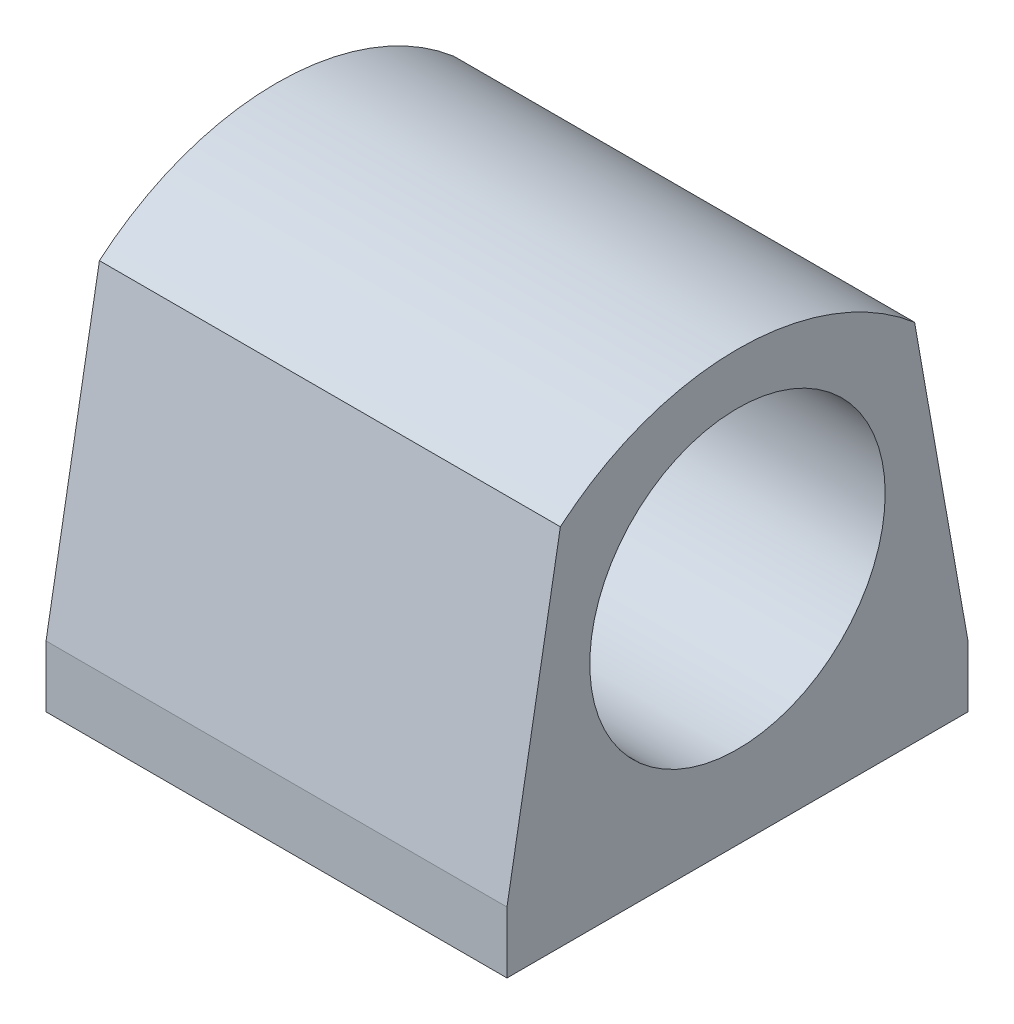
SolidWorks part; units mm, degrees
material "ABS"
ref_plane "Front Plane" through (0, 0, 0) normal (0, 0, 1) x (1, 0, 0)
ref_plane "Top Plane" through (0, 0, 0) normal (0, 1, 0) x (1, 0, 0)
ref_plane "Right Plane" through (0, 0, 0) normal (1, 0, 0) x (0, 0, -1)
sketch "Sketch2" plane through (0, 0, 0) normal (0, 1, 0) x (1, 0, 0)
  line L1 (-19.05, -19.05) -> (19.05, -19.05)
  line L2 (-19.05, -19.05) -> (-19.05, 19.05)
  line L3 (-19.05, 19.05) -> (19.05, 19.05)
  line L4 (19.05, -19.05) -> (19.05, 19.05)
  line L5 (-19.05, -19.05) -> (19.05, 19.05) construction
  line L6 (-19.05, 19.05) -> (19.05, -19.05) construction
  point P0 (0, 0)
  dimension "D1" = 38.1
  dimension "D2" = 38.1
extrude "Boss-Extrude1" add sketch "Sketch2" along normal blind 5.08
sketch "Sketch3" plane through (19.05, 0, 0) normal (1, 0, 0) x (0, 0, -1)
  line L0 (-19.05, 5.08) -> (-14.6393, 30.0941)
  line L1 (19.05, 5.08) -> (14.6393, 30.0941)
  line L3 (-19.05, 5.08) -> (19.05, 5.08) construction
  line L4 (19.05, 5.08) -> (-19.05, 5.08)
  arc A1 (-14.6393, 30.0941) -> (14.6393, 30.0941) centre (0, 12.91) cw
  dimension "D1" = 80
  dimension "D2" = 80
extrude "Boss-Extrude3" add sketch "Sketch3" along direction (1, 0, 0) on the side against the normal through all
sketch "Sketch5" plane through (19.05, 0, 0) normal (1, 0, 0) x (0, 0, -1)
  line L0 (-19.05, 0) -> (19.05, 0) construction
  circle A0 centre (0, 19.05) radius 12.2085
  dimension "D1" = 19.05
extrude "Cut-Extrude1" cut sketch "Sketch5" against normal through all
sketch "Sketch6" plane through (0, 0, -19.05) normal (0, 0, -1) x (-1, 0, 0)
  line L0 (19.05, 0) -> (19.05, -19.05)
  line L1 (19.05, -19.05) -> (0, 0)
  line L2 (-19.05, 0) -> (19.05, 0) construction
  line L3 (0, 0) -> (19.05, 0)
  dimension "D1" = 19.05
extrude "Boss-Extrude4" add sketch "Sketch6" against normal blind 5.08
